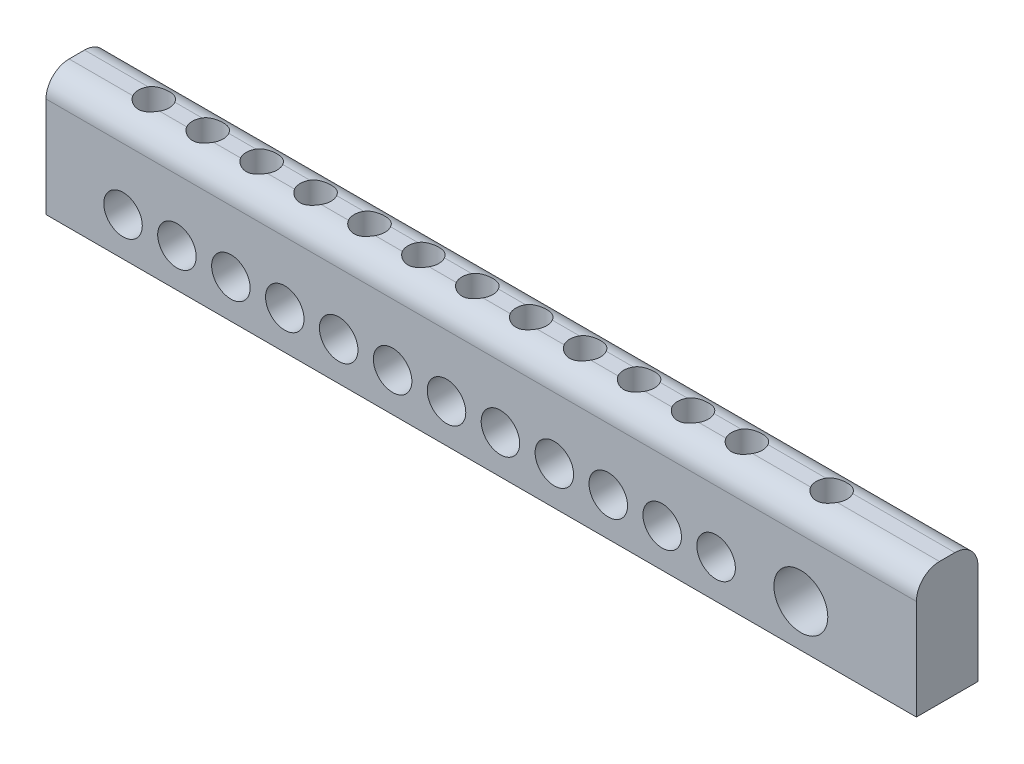
SolidWorks part; units mm, degrees
ref_plane "Plan de face" through (0, 0, 0) normal (0, 0, 1) x (1, 0, 0)
ref_plane "Plan de dessus" through (0, 0, 0) normal (0, 1, 0) x (1, 0, 0)
ref_plane "Plan de droite" through (0, 0, 0) normal (1, 0, 0) x (0, 0, -1)
sketch "Esquisse1" plane through (0, 0, 0) normal (0, 0, 1) x (1, 0, 0)
  line L1 (0, 0) -> (113, 0)
  line L2 (0, 0) -> (0, -16)
  line L3 (0, -16) -> (113, -16)
  line L4 (113, 0) -> (113, -16)
  dimension "D1" = 113
  dimension "D2" = 16
extrude "Extrusion1" add sketch "Esquisse1" along normal blind 8
fillet "Congé2" radius 3 2 edges at (56.5, 0, 0) (56.5, 0, 8)
sketch "Esquisse2" plane through (0, 0, 8) normal (0, 0, 1) x (1, 0, 0)
  line L0 (0, -16) -> (113, -16) construction
  line L1 (0, -3) -> (0, -16) construction
  circle A0 centre (10, -11) radius 2.5
  dimension "D1" = 5
  dimension "D2" = 5
  dimension "D3" = 10
extrude "Extrusion2" cut sketch "Esquisse2" against normal blind 7
pattern_linear "Répétition linéaire1" count 12 spacing 7 along (1, 0, 0) of "Extrusion2"
sketch "Esquisse3" plane through (0, 0, 8) normal (0, 0, 1) x (1, 0, 0)
  line L0 (113, -16) -> (113, -3) construction
  line L1 (0, -16) -> (113, -16) construction
  circle A0 centre (98, -10.5) radius 3.5
  dimension "D1" = 7
  dimension "D2" = 15
  dimension "D3" = 5.5
extrude "Extrusion3" cut sketch "Esquisse3" against normal blind 7
sketch "Esquisse4" plane through (0, 0, 0) normal (0, 1, 0) x (1, 0, 0)
  line L0 (0, -8) -> (0, 0) construction
  line L1 (113, -8) -> (0, -8) construction
  circle A0 centre (10, -4) radius 2
  point P2 (0, -4)
  dimension "D1" = 4
  dimension "D2" = 10
  dimension "D3" = 4
extrude "Extrusion4" cut sketch "Esquisse4" against normal blind 10
pattern_linear "Répétition linéaire2" count 12 spacing 7 along (1, 0, 0) of "Extrusion4"
sketch "Esquisse5" plane through (0, 0, 0) normal (0, 1, 0) x (-1, 0, 0)
  line L0 (-113, 5) -> (-113, 3) construction
  line L1 (0, 0) -> (-113, 0) construction
  circle A0 centre (-98, 4) radius 2
  dimension "D1" = 4
  dimension "D2" = 15
  dimension "D3" = 4
extrude "Extrusion5" cut sketch "Esquisse5" against normal blind 10
